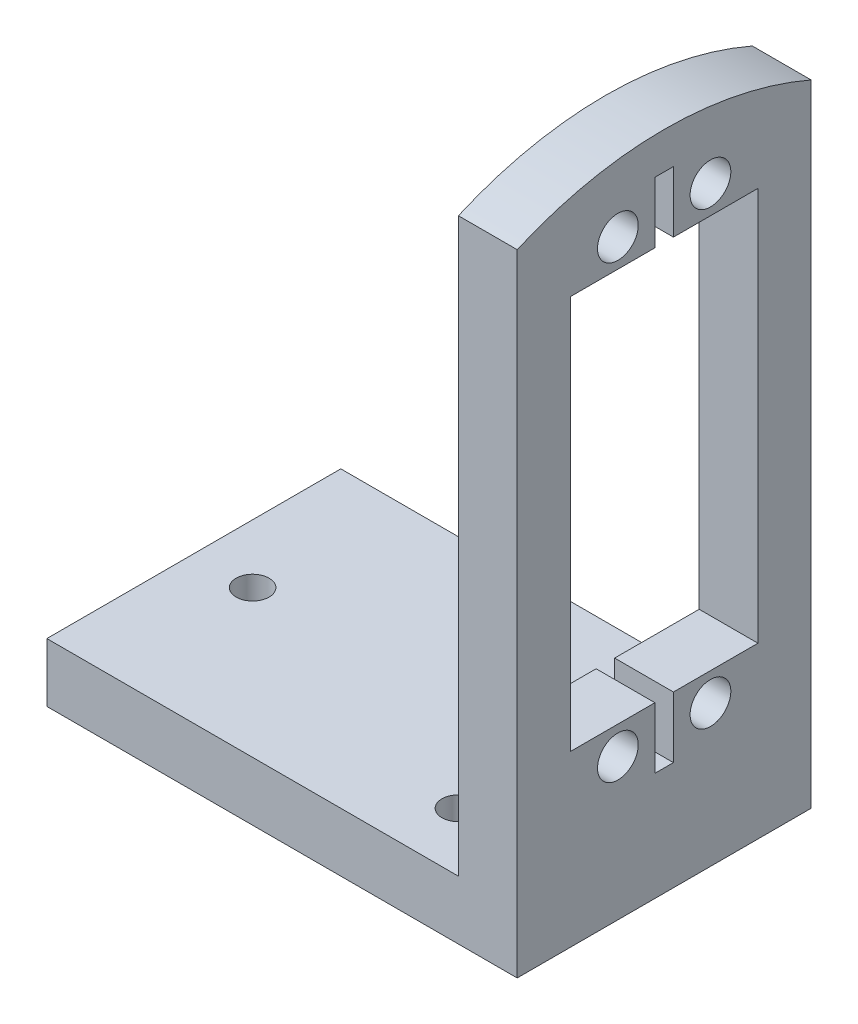
SolidWorks part; units mm, degrees
ref_plane "Front Plane" through (0, 0, 0) normal (0, 0, 1) x (1, 0, 0)
ref_plane "Top Plane" through (0, 0, 0) normal (0, 1, 0) x (1, 0, 0)
ref_plane "Right Plane" through (0, 0, 0) normal (1, 0, 0) x (0, 0, -1)
sketch "Sketch3" plane through (0, 0, 0) normal (1, 0, 0) x (0, 0, -1)
  line L0 (5.748, 54.5075) -> (26.002, 11.9625) construction
  line L1 (0, 0) -> (31.75, 0)
  line L2 (0, 0) -> (0, 67.2075)
  line L3 (0, 67.2075) -> (31.75, 67.2075)
  line L4 (31.75, 0) -> (31.75, 67.2075)
  line L5 (5.748, 54.5075) -> (14.875, 54.5075)
  line L6 (5.748, 54.5075) -> (5.748, 11.9625)
  line L7 (5.748, 11.9625) -> (14.875, 11.9625)
  line L8 (26.002, 54.5075) -> (26.002, 11.9625)
  line L9 (26.002, 54.5075) -> (5.748, 11.9625) construction
  line L10 (10.875, 57.535) -> (20.875, 8.935) construction
  line L11 (10.875, 8.935) -> (20.875, 57.535) construction
  line L12 (16.875, 11.9625) -> (26.002, 11.9625)
  line L13 (14.875, 11.9625) -> (14.875, 5.3585)
  line L14 (14.875, 5.3585) -> (16.875, 5.3585)
  line L15 (16.875, 11.9625) -> (16.875, 5.3585)
  line L16 (15.875, 33.235) -> (-939.9401, 33.235) construction
  line L17 (14.875, 61.1115) -> (16.875, 61.1115)
  line L18 (14.875, 54.5075) -> (14.875, 61.1115)
  line L19 (16.875, 54.5075) -> (16.875, 61.1115)
  line L20 (16.875, 54.5075) -> (26.002, 54.5075)
  circle A0 centre (10.875, 8.935) radius 2.2
  circle A1 centre (20.875, 8.935) radius 2.2
  circle A2 centre (10.875, 57.535) radius 2.2
  circle A3 centre (20.875, 57.535) radius 2.2
  point P13 (15.875, 5.3585)
  point P22 (15.875, 33.235)
  point P23 (15.875, 33.235)
  point P32 (15.875, 23.6075)
  point P33 (15.875, 42.8625)
  point P34 (15.875, 0)
  dimension "D3" = 4.4
  dimension "D1" = 10
  dimension "D2" = 48.6
  dimension "D4" = 42.545
  dimension "D5" = 20.254
  dimension "D6" = 2
  dimension "D7" = 6.604
  dimension "D12" = 12.7
  dimension "D10" = 31.75
  dimension "D8" = 30.9
  dimension "D9" = 42.8625
extrude "Boss-Extrude1" add sketch "Sketch3" along normal blind 6.35
sketch "Sketch5" plane through (6.35, 0, 0) normal (1, 0, 0) x (0, 0, -1)
  line L1 (0, 0) -> (31.75, 0)
  line L2 (0, 0) -> (0, -6.35)
  line L3 (0, -6.35) -> (31.75, -6.35)
  line L4 (31.75, 0) -> (31.75, -6.35)
  dimension "D1" = 6.35
extrude "Boss-Extrude2" add sketch "Sketch5" against normal blind 50.8
sketch "Sketch6" plane through (0, 0, 0) normal (0, 1, 0) x (1, 0, 0)
  line L0 (-44.45, 0) -> (0, 0) construction
  line L2 (-44.45, 31.75) -> (-44.45, 0) construction
  line L3 (0, 15.875) -> (-33.0413, 15.875) construction
  line L5 (0, 31.75) -> (0, 0) construction
  circle A0 centre (-6.35, 6.35) radius 1.777
  circle A2 centre (-38.1, 15.875) radius 1.777
  circle A3 centre (-6.35, 25.4) radius 1.777
  dimension "D1" = 3.554
  dimension "D2" = 6.35
  dimension "D4" = 6.35
  dimension "D3" = 6.35
extrude "Cut-Extrude1" cut sketch "Sketch6" against normal through all
sketch "Sketch7" plane through (6.35, 0, 0) normal (1, 0, 0) x (0, 0, -1)
  line L0 (31.75, 67.2075) -> (0, 67.2075) construction
  line L1 (0, -6.35) -> (31.75, -6.35) construction
  line L2 (0, 61.7742) -> (0, 82.7489)
  line L3 (0, 67.2075) -> (0, -6.35) construction
  line L4 (0, 82.7489) -> (31.75, 82.7489)
  line L5 (31.75, 82.7489) -> (31.75, 61.7742)
  line L6 (31.75, -6.35) -> (31.75, 67.2075) construction
  arc A0 (31.75, 61.7742) -> (0, 61.7742) centre (15.875, 25.4) ccw
  point P6 (15.875, 67.2075)
  dimension "D2" = 79.375
  dimension "D1" = 31.75
extrude "Cut-Extrude2" cut sketch "Sketch7" against normal through all
equation "\"D1@Sketch6\" = 3.3mm + \"normtol\""
equation "\"tighttol\" = 0.005in"
equation "\"normtol\" = 0.01in"
equation "\"loosetol\" = 0.02in"
equation "\"Fry height\"= 0.5in"
equation "\"Fry spacing\"= 0.5625in"
equation "\"Potato width\"= \"Fry spacing\" * 4"
equation "\"Potato length\"= 80mm"
equation "\"top robot surface separation\" = 0.6875"
equation "\"D9@Sketch3\"=1+\"top robot surface separation\""
